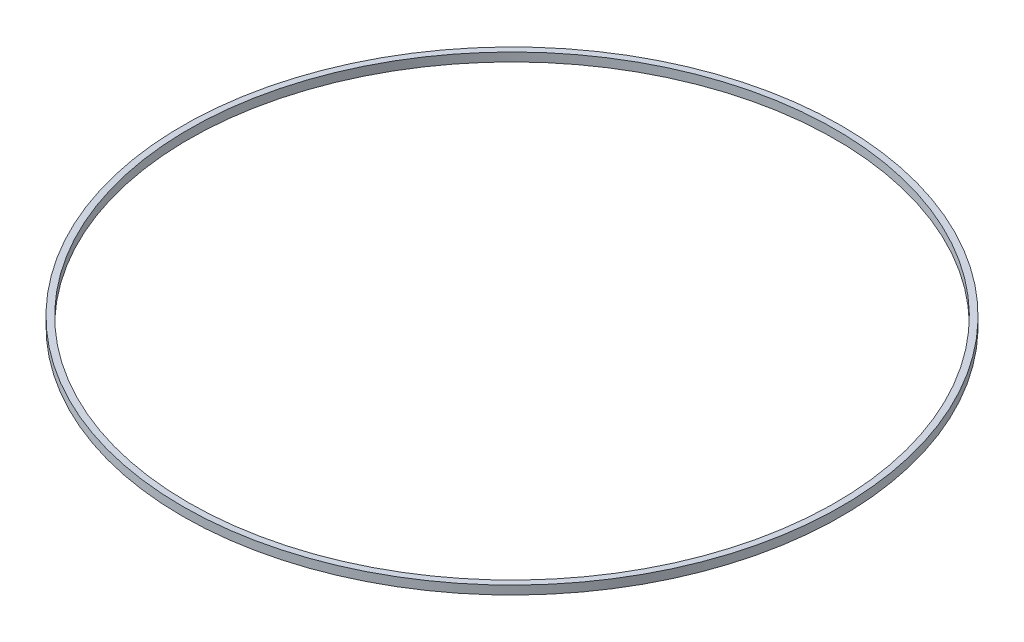
SolidWorks part; units mm, degrees
ref_plane "Front Plane" through (0, 0, 0) normal (0, 0, 1) x (1, 0, 0)
ref_plane "Top Plane" through (0, 0, 0) normal (0, 1, 0) x (1, 0, 0)
ref_plane "Right Plane" through (0, 0, 0) normal (1, 0, 0) x (0, 0, -1)
sketch "Sketch1" plane through (0, 0, 0) normal (0, 1, 0) x (1, 0, 0)
  circle A0 centre (0, 0) radius 52.52
  circle A1 centre (0, 0) radius 53.52
  dimension "D1" = 105.04
  dimension "D2" = 1
extrude "Boss-Extrude1" add sketch "Sketch1" along normal blind 1.4
